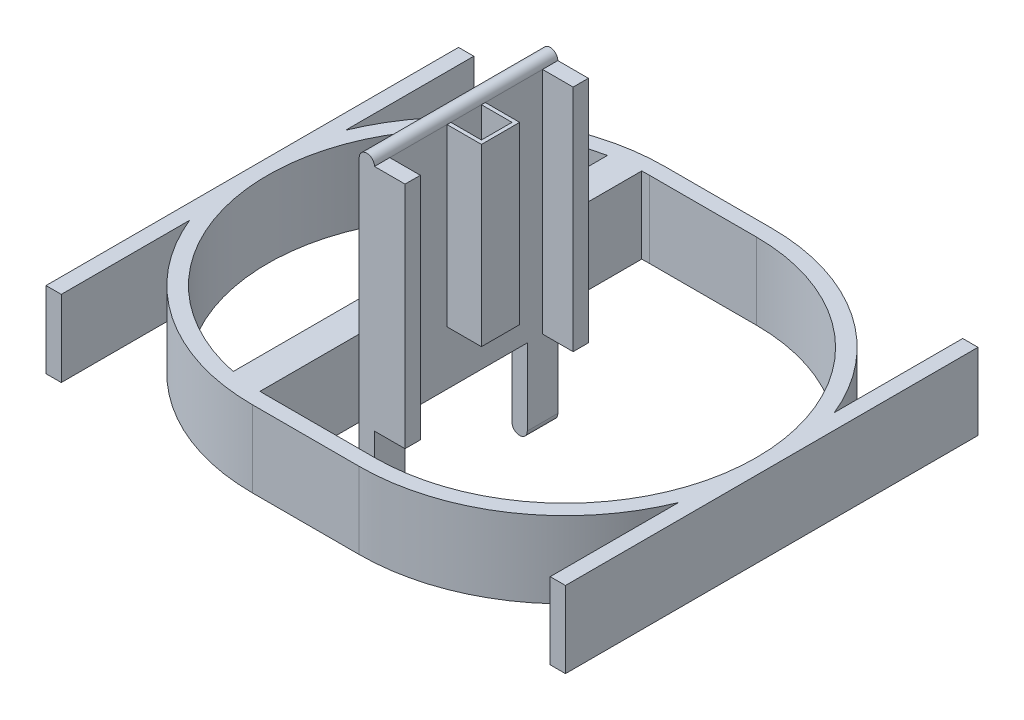
SolidWorks part; units mm, degrees
ref_plane "Front" through (0, 0, 0) normal (0, 0, 1) x (1, 0, 0)
ref_plane "Top" through (0, 0, 0) normal (0, 1, 0) x (1, 0, 0)
ref_plane "Right" through (0, 0, 0) normal (1, 0, 0) x (0, 0, -1)
sketch "草图2" plane through (0, 0, 0) normal (0, 1, 0) x (1, 0, 0)
  line L0 (-7, 0) -> (7, 0) construction
  line L3 (-7, 0) -> (7, 0) construction
  line L4 (-7, 27) -> (7, 27)
  line L5 (-7, -27) -> (7, -27)
  line L6 (-38.2984, -16) -> (-28.7486, -16) construction
  line L8 (-35.4759, -14) -> (-30.0868, -14) construction
  line L10 (23.5227, -16) -> (40.8516, -16) construction
  line L11 (25.2483, -14) -> (35.6561, -14) construction
  line L12 (-7, 0) -> (7, 0) construction
  line L15 (-8, 31.8677) -> (-8, 21.5639) construction
  line L16 (-12, 30.5999) -> (-12, 19.6214) construction
  line L19 (-12, -19.6214) -> (-12, -38.5553) construction
  line L20 (-8, -21.5639) -> (-8, -42.1638) construction
  line L21 (-7, 0) -> (7, 0) construction
  line L22 (-7, 25) -> (7, 25)
  line L23 (-7, -25) -> (7, -25)
  line L24 (-8, 24.98) -> (-8, -24.98)
  line L25 (-12, -24.4949) -> (-12, 24.4949)
  arc A4 (-7, 27) -> (-7, -27) centre (-7, 0) ccw
  arc A5 (7, -27) -> (7, 27) centre (7, 0) ccw
  arc A12 (-7, 25) -> (-8, 24.98) centre (-7, 0) ccw
  arc A13 (7, -25) -> (7, 25) centre (7, 0) ccw
  arc A14 (-8, -24.98) -> (-7, -25) centre (-7, 0) ccw
  arc A15 (-12, 24.4949) -> (-12, -24.4949) centre (-7, 0) ccw
  point P3 (0, 0)
  point P7 (0, 0)
  point P10 (0, 0)
  point P21 (0, 0)
  dimension "D1" = 16
  dimension "D2" = 8
  dimension "D3" = 4
extrude "凸台-拉伸1" add sketch "草图2" along normal blind 10
sketch "草图9" plane through (-8, 0, 0) normal (1, 0, 0) x (0, 0, -1)
  line L0 (-27, 0) -> (27, 0) construction
  line L1 (-12, 30) -> (12, 30)
  line L2 (-12, 30) -> (-12, -10)
  line L3 (-12, -10) -> (12, -10)
  line L4 (12, 30) -> (12, -10)
  dimension "D1" = 24
  dimension "D2" = 40
  dimension "D3" = 10
  dimension "D4" = 12
extrude "凸台-拉伸5" add sketch "草图9" along normal blind 2
sketch "草图10" plane through (0, 0, -12) normal (0, 0, -1) x (-1, 0, 0)
  line L0 (6, 30) -> (8, 30) construction
  line L1 (6, -10) -> (8, -10) construction
  circle A0 centre (7, 30) radius 1
  circle A1 centre (7, -10) radius 1
extrude "凸台-拉伸6" add sketch "草图10" against normal blind 24
sketch "草图11" plane through (-6, 0, 0) normal (1, 0, 0) x (0, 0, -1)
  line L1 (-8, -15.1521) -> (8, -15.1521)
  line L2 (-8, -15.1521) -> (-8, 0)
  line L3 (-8, 0) -> (8, 0)
  line L4 (8, -15.1521) -> (8, 0)
  line L6 (0, 0) -> (0, -21.1916) construction
  dimension "D1" = 16
  dimension "D2" = 8
extrude "切除-拉伸2" cut sketch "草图11" against normal blind 24
sketch "草图12" plane through (-6, 0, 0) normal (1, 0, 0) x (0, 0, -1)
  line L10 (12, 30) -> (10, 30)
  line L11 (12, 30) -> (12, 0)
  line L12 (12, 0) -> (10, 0)
  line L13 (10, 30) -> (10, 0)
  line L14 (-12, 30) -> (-10, 30)
  line L15 (-12, 30) -> (-12, 0)
  line L16 (-12, 0) -> (-10, 0)
  line L17 (-10, 30) -> (-10, 0)
  dimension "D1" = 2
  dimension "D2" = 2
extrude "凸台-拉伸7" add sketch "草图12" along normal blind 4
sketch "草图13" plane through (0, 30, 0) normal (0, 1, 0) x (1, 0, 0)
  line L0 (-6, 10) -> (-6, -10) construction
  line L1 (-6, 2) -> (-2, 2)
  line L2 (-6, 2) -> (-6, -2)
  line L3 (-6, -2) -> (-2, -2)
  line L4 (-2, 2) -> (-2, -2)
  line L5 (-2, 2) -> (-6, 2) construction
  line L7 (-6.5, 2.5) -> (-1.5, 2.5)
  line L8 (-6.5, 2.5) -> (-6.5, -2.5)
  line L9 (-6.5, -2.5) -> (-1.5, -2.5)
  line L10 (-1.5, 2.5) -> (-1.5, -2.5)
  dimension "D1" = 5
  dimension "D2" = 0.5
  dimension "D3" = 5
  dimension "D4" = 0.5
sketch "草图14" plane through (-6, 0, 0) normal (1, 0, 0) x (0, 0, -1)
  line L0 (-2, 7.0682) -> (-2, 30)
  line L1 (-2, 22.9706) -> (-2, 6.9706) construction
  line L2 (2, 30) -> (-2, 30) construction
sweep "扫描3" add profiles "草图13" path "草图14"
sketch "草图15" plane through (0, 0, 0) normal (0, -1, 0) x (1, 0, 0)
  line L0 (36.7777, 0) -> (-55.0297, 0) construction
  line L1 (31.5597, -27) -> (-31.9085, -27) construction
  line L2 (-38.984, 27) -> (44.5315, 27) construction
  line L3 (-33.909, -27) -> (-45.9854, -27) construction
  line L13 (-34, 27) -> (-32, 27)
  line L14 (-34, 27) -> (-34, -27)
  line L15 (-34, -27) -> (-32, -27)
  line L16 (-32, 27) -> (-32, -27)
  line L17 (34, 27) -> (32, 27)
  line L18 (34, 27) -> (34, -27)
  line L19 (34, -27) -> (32, -27)
  line L20 (32, 27) -> (32, -27)
  arc A0 (-7, 27) -> (-7, -27) centre (-7, 0) ccw construction
  arc A1 (7, -27) -> (7, 27) centre (7, 0) ccw construction
  point P5 (-34, 0)
  point P6 (34, 0)
  point P7 (33.8961, -1)
  point P12 (-33.909, -1)
  dimension "D1" = 2
  dimension "D2" = 2
extrude "凸台-拉伸8" add sketch "草图15" against normal blind 10
